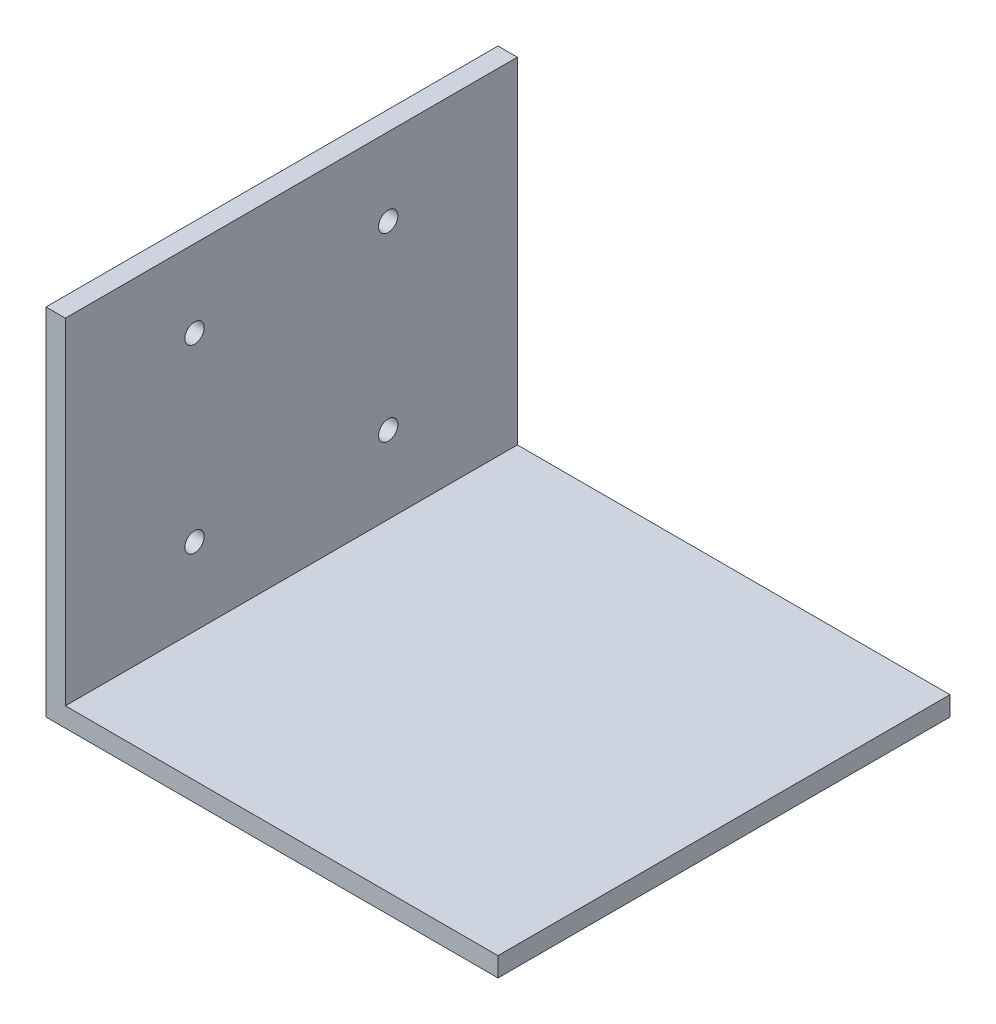
SolidWorks part; units mm, degrees
ref_plane "Front Plane" through (0, 0, 0) normal (0, 0, 1) x (1, 0, 0)
ref_plane "Top Plane" through (0, 0, 0) normal (0, 1, 0) x (1, 0, 0)
ref_plane "Right Plane" through (0, 0, 0) normal (1, 0, 0) x (0, 0, -1)
sketch "Sketch1" plane through (0, 0, 0) normal (0, 0, 1) x (1, 0, 0)
  line L0 (0, 0) -> (0, 55)
  line L1 (0, 55) -> (3, 55)
  line L2 (3, 55) -> (3, 3)
  line L3 (3, 3) -> (70, 3)
  line L4 (70, 3) -> (70, 0)
  line L5 (70, 0) -> (0, 0)
  dimension "D1" = 3
  dimension "D2" = 3
  dimension "D3" = 70
  dimension "D4" = 55
extrude "Boss-Extrude1" add sketch "Sketch1" along normal blind 70
sketch "Sketch2" plane through (3, 0, 0) normal (1, 0, 0) x (0, 0, -1)
  line L0 (-70, 55) -> (0, 55) construction
  line L4 (-70, 3) -> (-70, 55) construction
  line L5 (-35, 55) -> (-35, 3) construction
  line L6 (-70, 3) -> (0, 3) construction
  line L7 (-70, 29) -> (0, 29) construction
  line L8 (0, 3) -> (0, 55) construction
  circle A0 centre (-50, 43) radius 1.5
  circle A1 centre (-20, 43) radius 1.5
  circle A2 centre (-20, 15) radius 1.5
  circle A3 centre (-50, 15) radius 1.5
  dimension "D1" = 3
  dimension "D2" = 12
  dimension "D3" = 20
extrude "Cut-Extrude1" cut sketch "Sketch2" against normal blind 70
